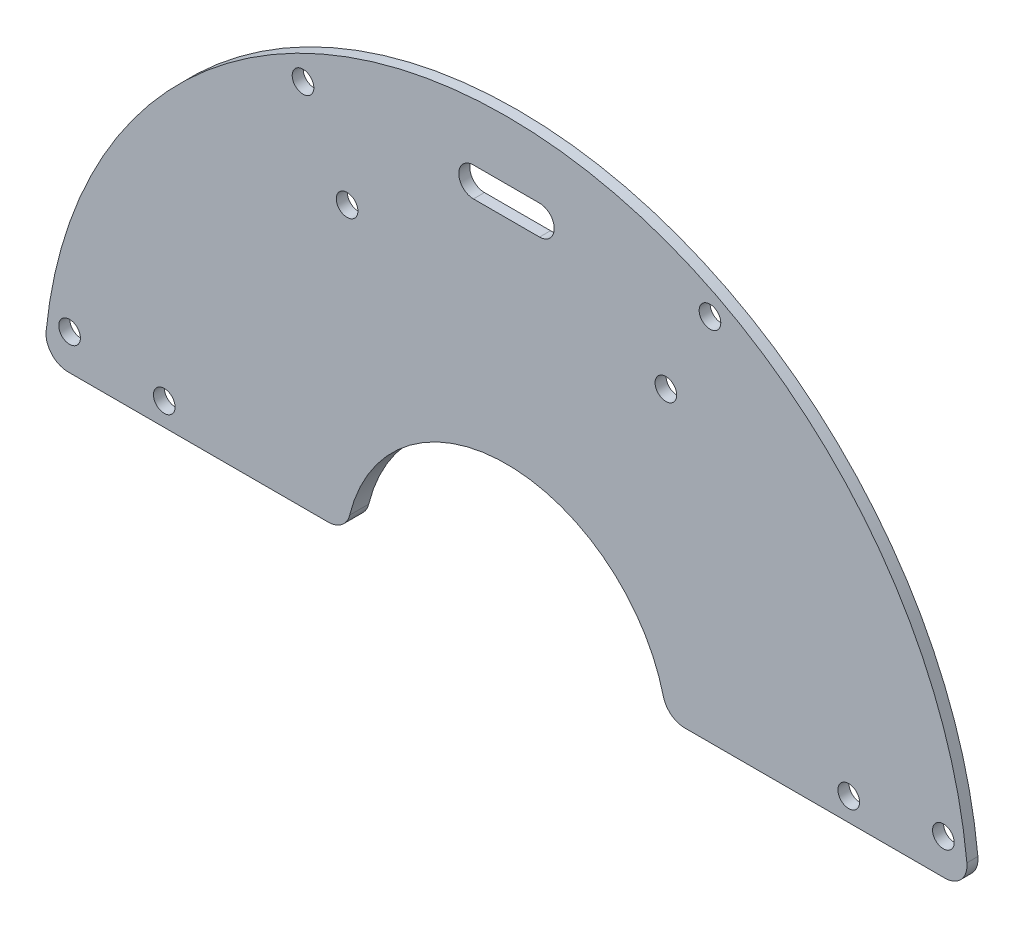
SolidWorks part; units mm, degrees
ref_plane "Front Plane" through (0, 0, 0) normal (0, 0, 1) x (1, 0, 0)
ref_plane "Top Plane" through (0, 0, 0) normal (0, 1, 0) x (1, 0, 0)
ref_plane "Right Plane" through (0, 0, 0) normal (1, 0, 0) x (0, 0, -1)
sketch "Sketch1" plane through (0, 0, 0) normal (1, 0, 0) x (0, 0, -1)
  line L0 (0, 22) -> (0, 63)
  line L1 (0, 63) -> (1.5, 63)
  line L2 (1.5, 63) -> (1.5, 35)
  line L3 (1.5, 35) -> (2.6, 32.5)
  line L4 (2.6, 32.5) -> (2.6, 22)
  line L5 (2.6, 22) -> (0, 22)
  line L6 (0, 0) -> (99.7165, 0) construction
  dimension "D1" = 63
  dimension "D2" = 22
  dimension "D3" = 1.5
  dimension "D4" = 2.6
  dimension "D5" = 35
  dimension "D6" = 2.5
revolve "Revolve1" add sketch "Sketch1" angle 360 about L6
sketch "Sketch2" plane through (0, 0, 0) normal (0, 0, 1) x (1, 0, 0)
  line L0 (0, 0) -> (-115.6955, 0) construction
  line L2 (-99.6906, 3) -> (98.3094, 3)
  line L3 (-99.6906, 3) -> (-99.6906, -100.3213)
  line L4 (-99.6906, -100.3213) -> (98.3094, -100.3213)
  line L5 (98.3094, 3) -> (98.3094, -100.3213)
  dimension "D1" = 3
extrude "Cut-Extrude1" cut sketch "Sketch2" against normal through all
fillet "Fillet1" radius 5 2 edges at (0, 32.5, -2.6) (0, 35, -1.5)
fillet "Fillet2" radius 3 4 edges at (-21.7945, 3, -1.3) (21.7945, 3, -1.3) (-62.9285, 3, -0.75) (62.9285, 3, -0.75)
hole_wizard "#4 Clearance Hole1" positions "Sketch4" profile "Sketch3" hole size "#4" standard "ANSI Inch"
sketch "Sketch4" plane through (0, 0, 0) normal (0, 0, 1) x (1, 0, 0)
  line L0 (0, 0) -> (-17.0673, 2.247) construction
  line L1 (0, 0) -> (-24.1828, 0) construction
  point P1 (-59.4867, 7.8316)
  point P12 (-46.5979, 6.1347)
  dimension "D1" = 7.5
  dimension "D2" = 60
  dimension "D3" = 47
sketch "Sketch3" plane through (-59.4867, 7.8316, 0) normal (1, 0, 0) x (0, -1, 0)
  line L0 (0, 0) -> (0, 136.7752)
  line L1 (0, 136.7752) -> (1.4732, 135.89)
  line L2 (1.4732, 135.89) -> (1.4732, 0)
  line L5 (1.4732, 0) -> (0, 0)
  line L10 (0, 136.7752) -> (-1.4732, 135.89) construction
  line L11 (0, -6.35) -> (0, 107.95) construction
  dimension "Hole Dia." = 2.9464
  dimension "Hole Depth" = 135.89
  dimension "Drill Angle" = 118
pattern_circular "CirPattern1" count 4 every 55 about axis through (0, 0, 0) along (0, 0, 1) of "#4 Clearance Hole1"
sketch "Sketch5" plane through (0, 0, 0) normal (0, 0, 1) x (1, 0, 0)
  line L0 (0, 0) -> (12.6074, 0) construction
  line L1 (0, 0) -> (0, 12.3859) construction
  line L2 (-4.5, 53) -> (4.5, 53) construction
  line L3 (-4.5, 55) -> (4.5, 55)
  line L4 (-4.5, 51) -> (4.5, 51)
  arc A0 (-4.5, 55) -> (-4.5, 51) centre (-4.5, 53) ccw
  arc A1 (4.5, 51) -> (4.5, 55) centre (4.5, 53) ccw
  point P6 (0, 53)
  dimension "D1" = 53
  dimension "D2" = 4
  dimension "D3" = 9
extrude "Cut-Extrude2" cut sketch "Sketch5" against normal through all
